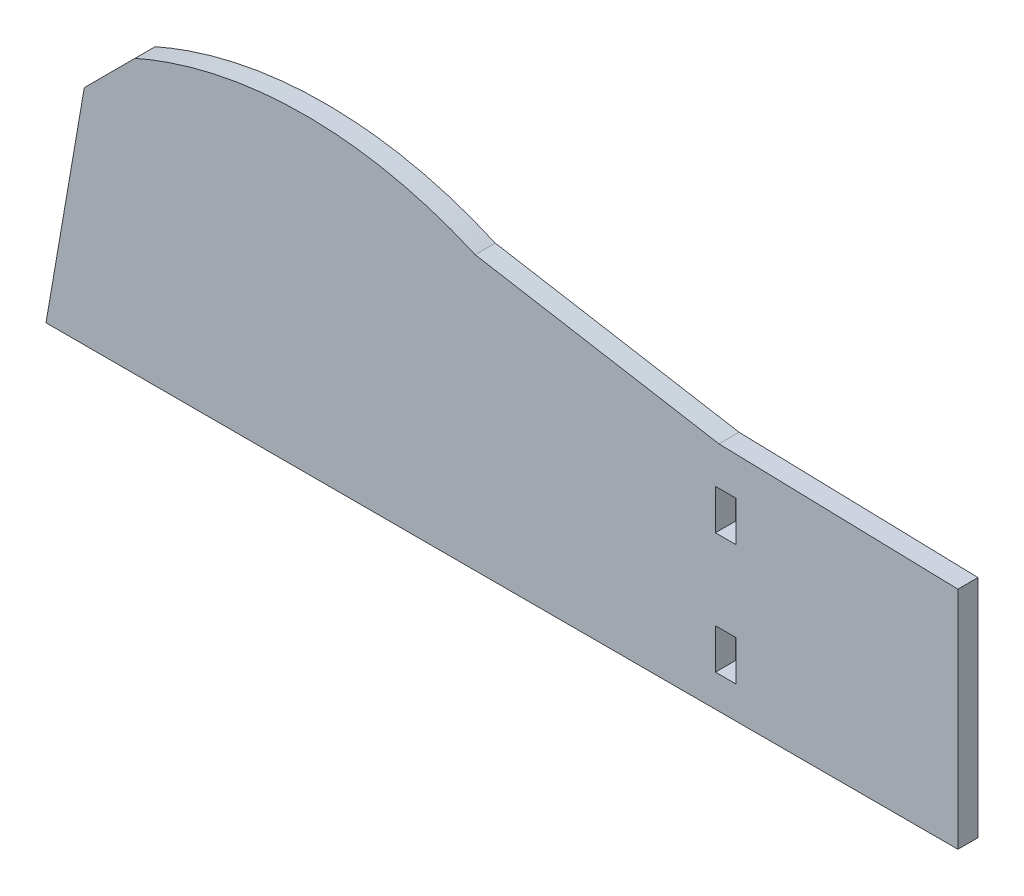
SolidWorks part; units mm, degrees
ref_plane "Front Plane" through (0, 0, 0) normal (0, 0, 1) x (1, 0, 0)
ref_plane "Top Plane" through (0, 0, 0) normal (0, 1, 0) x (1, 0, 0)
ref_plane "Right Plane" through (0, 0, 0) normal (1, 0, 0) x (0, 0, -1)
sketch "Sketch1" plane through (0, 0, 0) normal (0, 0, 1) x (1, 0, 0)
  line L0 (-76.2, 43.18) -> (-37.7134, 36.5669)
  line L1 (-37.7134, 36.5669) -> (0, 35.56)
  line L2 (-129.8924, 43.18) -> (-137.8958, 35.1766)
  line L3 (-137.8958, 35.1766) -> (-143.9401, 0)
  line L4 (0, 0) -> (-143.9401, 0)
  line L5 (0, 35.56) -> (0, 0)
  spline S0 degree 3 poles (-129.8924, 43.18) (-123.6329, 45.956) (-114.6257, 48.3623) (-103.248, 48.9721) (-95.5225, 48.5934) (-86.4115, 47.0275) (-79.7261, 44.7408) (-76.2, 43.18) knots 0 0 0 0 0.371233 0.499907 0.617609 0.790714 1 1 1 1
  dimension "D1" = 35.56
extrude "Boss-Extrude1" add sketch "Sketch1" along normal blind 3.175
sketch "Sketch3" plane through (0, 0, 3.175) normal (0, 0, 1) x (1, 0, 0)
  line L1 (-38.2778, 30.48) -> (-35.052, 30.48)
  line L2 (-38.2778, 30.48) -> (-38.2778, 24.13)
  line L3 (-38.2778, 24.13) -> (-35.052, 24.13)
  line L4 (-35.052, 30.48) -> (-35.052, 24.13)
  line L5 (-38.2778, 30.48) -> (-35.052, 24.13) construction
  line L6 (-38.2778, 24.13) -> (-35.052, 30.48) construction
  line L7 (-38.2778, 11.43) -> (-35.052, 11.43)
  line L8 (-38.2778, 11.43) -> (-38.2778, 5.08)
  line L9 (-38.2778, 5.08) -> (-35.052, 5.08)
  line L10 (-35.052, 11.43) -> (-35.052, 5.08)
  line L11 (-38.2778, 11.43) -> (-35.052, 5.08) construction
  line L12 (-38.2778, 5.08) -> (-35.052, 11.43) construction
  line L13 (0, 0) -> (0, 35.56) construction
  line L14 (0, 17.78) -> (-72.7942, 17.78) construction
  point P0 (-36.6649, 27.305)
  point P5 (-36.6649, 8.255)
  dimension "D1" = 6.35
  dimension "D2" = 6.35
  dimension "D3" = 6.35
  dimension "D4" = 6.35
  dimension "D5" = 35.052
  dimension "D6" = 3.2258
  dimension "D7" = 3.2258
  dimension "D8" = 35.052
extrude "holes for tabs" cut sketch "Sketch3" against normal through all
